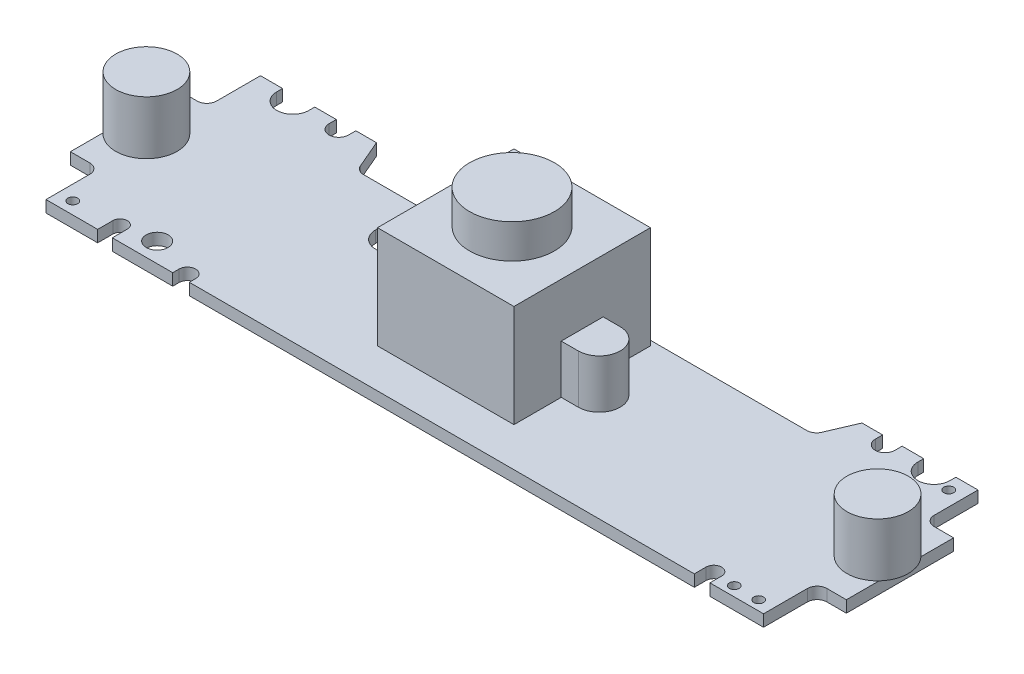
SolidWorks part; units mm, degrees
ref_plane "Front Plane" through (0, 0, 0) normal (0, 0, 1) x (1, 0, 0)
ref_plane "Top Plane" through (0, 0, 0) normal (0, 1, 0) x (1, 0, 0)
ref_plane "Right Plane" through (0, 0, 0) normal (1, 0, 0) x (0, 0, -1)
sketch "Sketch1" plane through (0, 0, 0) normal (0, 1, 0) x (1, 0, 0)
  line L0 (-36.8, -11) -> (-31.5, -11)
  line L1 (36.8, -11) -> (36.8, -6.5)
  line L2 (37.8, -5.5) -> (39.8, -5.5)
  line L3 (39.8, -5.5) -> (39.8, 5.5)
  line L4 (39.8, 5.5) -> (37.8, 5.5)
  line L5 (36.8, 6.5) -> (36.8, 11)
  line L6 (36.8, 11) -> (34.5316, 11)
  line L7 (24.9, 11) -> (23.6597, 8.1061)
  line L8 (22.7406, 7.5) -> (-13.8, 7.5)
  line L9 (-13.8, 7.5) -> (-13.8, 3.1942)
  line L10 (-34.5316, 11) -> (-34.5316, 10.4)
  line L11 (-17.2, 3.1942) -> (-17.2, 7.5)
  line L12 (-17.2, 7.5) -> (-22.7406, 7.5)
  line L13 (-24.9, 11) -> (-27.0168, 11)
  line L14 (-36.8, 11) -> (-36.8, 6.5)
  line L15 (-37.8, 5.5) -> (-39.8, 5.5)
  line L16 (-39.8, 5.5) -> (-39.8, -5.5)
  line L17 (-39.8, -5.5) -> (-37.8, -5.5)
  line L18 (-36.8, -6.5) -> (-36.8, -11)
  line L19 (-36.8, -11) -> (-31.5, -11) construction
  line L20 (-23.6597, 8.1061) -> (-24.9, 11)
  line L21 (-29.0168, 11) -> (-31.2316, 11)
  line L22 (-31.2316, 10.4) -> (-31.2316, 11)
  line L24 (-29.0168, 11) -> (-29.0168, 10.25)
  line L25 (0, 0) -> (0, 50000) construction
  line L26 (-27.0168, 10.25) -> (-27.0168, 11)
  line L27 (-34.5316, 11) -> (-36.8, 11)
  line L28 (27.0168, 10.25) -> (27.0168, 11)
  line L29 (29.0168, 11) -> (29.0168, 10.25)
  line L30 (31.2316, 10.4) -> (31.2316, 11)
  line L31 (34.5316, 11) -> (34.5316, 10.4)
  line L32 (27.0168, 11) -> (24.9, 11)
  line L33 (31.2316, 11) -> (29.0168, 11)
  line L34 (-31.5, -11) -> (-31.5, -9.45)
  line L36 (-30, -9.45) -> (-30, -11)
  line L37 (-23.8, -11) -> (-23.8, -10.35)
  line L39 (-22.1, -10.35) -> (-22.1, -11)
  line L40 (31.3, -11) -> (31.3, -9.8)
  line L42 (29.7, -9.8) -> (29.7, -11)
  line L43 (31.3, -11) -> (36.8, -11)
  line L44 (-22.1, -11) -> (29.7, -11)
  line L45 (-30, -11) -> (-23.8, -11)
  arc A0 (-13.9482, 2.5) -> (-17.2, 3.1942) centre (-15.5, 3.1942) cw construction
  arc A1 (-17.2, 3.1942) -> (-13.8, 3.1942) centre (-15.5, 3.1942) ccw
  arc A2 (-28.0168, 9.25) -> (-29.0168, 10.25) centre (-28.0168, 10.25) cw construction
  arc A3 (-32.8816, 8.75) -> (-34.5316, 10.4) centre (-32.8816, 10.4) cw construction
  arc A4 (-34.5316, 10.4) -> (-31.2316, 10.4) centre (-32.8816, 10.4) ccw
  arc A5 (-29.0168, 10.25) -> (-27.0168, 10.25) centre (-28.0168, 10.25) ccw
  arc A6 (32.8816, 8.75) -> (34.5316, 10.4) centre (32.8816, 10.4) ccw construction
  arc A7 (28.0168, 9.25) -> (29.0168, 10.25) centre (28.0168, 10.25) ccw construction
  arc A8 (29.0168, 10.25) -> (27.0168, 10.25) centre (28.0168, 10.25) cw
  arc A9 (34.5316, 10.4) -> (31.2316, 10.4) centre (32.8816, 10.4) cw
  circle A10 centre (35.3, 9.5) radius 0.5
  arc A11 (-36.8, -6.5) -> (-37.8, -5.5) centre (-37.8, -6.5) ccw
  arc A12 (-37.8, 5.5) -> (-36.8, 6.5) centre (-37.8, 6.5) ccw
  arc A13 (37.8, -5.5) -> (36.8, -6.5) centre (37.8, -6.5) ccw
  arc A14 (37.8, 5.5) -> (36.8, 6.5) centre (37.8, 6.5) cw
  arc A15 (-22.7406, 7.5) -> (-23.6597, 8.1061) centre (-22.7406, 8.5) cw
  arc A16 (22.7406, 7.5) -> (23.6597, 8.1061) centre (22.7406, 8.5) ccw
  circle A17 centre (-35.3, -9.75) radius 0.5
  circle A18 centre (-27.4, -9) radius 1.125
  circle A19 centre (35.3, -10) radius 0.5
  circle A20 centre (32.8, -10) radius 0.5
  arc A21 (30.5, -9) -> (29.7, -9.8) centre (30.5, -9.8) ccw construction
  arc A22 (31.3, -9.8) -> (29.7, -9.8) centre (30.5, -9.8) ccw
  arc A23 (-22.95, -9.5) -> (-23.8, -10.35) centre (-22.95, -10.35) ccw construction
  arc A24 (-30.75, -8.7) -> (-31.5, -9.45) centre (-30.75, -9.45) ccw construction
  arc A25 (-30, -9.45) -> (-31.5, -9.45) centre (-30.75, -9.45) ccw
  arc A26 (-22.1, -10.35) -> (-23.8, -10.35) centre (-22.95, -10.35) ccw
  point P24 (-25.5275, 8)
  point P51 (25.5275, 8)
  dimension "D21" = 1.7
  dimension "D24" = 1
  dimension "D23" = 1.65
  dimension "D28" = 1
  dimension "D29" = 1.5
  dimension "D30" = 1.5
  dimension "D12" = 1
  dimension "D14" = 1
  dimension "D13" = 1
  dimension "D15" = 1
  dimension "D16" = 1
  dimension "D17" = 1
  dimension "D11" = 1
  dimension "D18" = 1
  dimension "D20" = 0.8
  dimension "D40" = 1
  dimension "D42" = 2.25
  dimension "D43" = 0.85
  dimension "D41" = 0.75
  dimension "D1" = 73.6
  dimension "D3" = 22
  dimension "D4" = 11
  dimension "D5" = 11
  dimension "D6" = 18.5
  dimension "D7" = 18.5
  dimension "D8" = 36.8
  dimension "D9" = 11.9
  dimension "D10" = 11.9
  dimension "D19" = 1.6
  dimension "D22" = 5
  dimension "D25" = 3.3
  dimension "D26" = 2.25
  dimension "D27" = 1.75
  dimension "D31" = 1.5
  dimension "D32" = 4
  dimension "D33" = 5.5
  dimension "D34" = 1
  dimension "D35" = 1
  dimension "D36" = 1.5
  dimension "D37" = 5.3
  dimension "D38" = 9.4
  dimension "D39" = 13
  dimension "D44" = 1.25
  dimension "D45" = 2
  dimension "D46" = 19.6
extrude "PCB" add sketch "Sketch1" along normal blind 1.2
sketch "Sketch2" plane through (0, 1.2, 0) normal (0, 1, 0) x (1, 0, 0)
  line L0 (-39.8, 5.5) -> (-39.8, -5.5) construction
  line L1 (39.8, -5.5) -> (39.8, 5.5) construction
  circle A0 centre (-37.5, 0) radius 3.15
  circle A1 centre (37.5, 0) radius 3.15
  dimension "D1" = 6.3
  dimension "D2" = 6.3
  dimension "D3" = 2.3
  dimension "D4" = 2.3
extrude "speakers" add sketch "Sketch2" along normal blind 5.5
sketch "Sketch3" plane through (0, 1.2, 0) normal (0, 1, 0) x (1, 0, 0)
  line L0 (-39.8, -2.1523) -> (-39.8, -5.5) construction
  line L1 (-6.8, -7) -> (7.2, -7)
  line L2 (-6.8, -7) -> (-6.8, 7)
  line L3 (-6.8, 7) -> (7.2, 7)
  line L4 (7.2, -7) -> (7.2, 7)
  line L5 (-6.8, -7) -> (7.2, 7) construction
  line L6 (-6.8, 7) -> (7.2, -7) construction
  line L7 (22.7406, 7.5) -> (-13.8, 7.5) construction
  point P0 (0.2, 0)
  dimension "D1" = 14
  dimension "D2" = 14
  dimension "D3" = 47
  dimension "D4" = 14.5
extrude "lens_mount" add sketch "Sketch3" along normal blind 10.5
sketch "Sketch4" plane through (0, 1.2, 0) normal (0, 1, 0) x (1, 0, 0)
  line L0 (-6.8, 7) -> (-6.8, -7) construction
  line L1 (-6.8, -7) -> (7.2, -7) construction
  line L3 (7.2, -7) -> (7.2, 7) construction
  line L4 (-8.55, 2.15) -> (8.95, 2.15)
  line L5 (-8.55, -2.15) -> (8.95, -2.15)
  arc A0 (-8.55, 2.15) -> (-8.55, -2.15) centre (-8.55, 0) ccw
  arc A1 (8.95, -2.15) -> (8.95, 2.15) centre (8.95, 0) ccw
  dimension "D2" = 4.3
  dimension "D3" = 4.3
  dimension "D1" = 1.75
  dimension "D4" = 7
  dimension "D5" = 1.75
extrude "lens_mouting_holes" add sketch "Sketch4" along normal blind 5
sketch "Sketch5" plane through (0, 11.7, 0) normal (0, 1, 0) x (1, 0, 0)
  circle A0 centre (0, 0) radius 4.35
  dimension "D1" = 8.7
extrude "lens" add sketch "Sketch5" along normal blind 3.5
